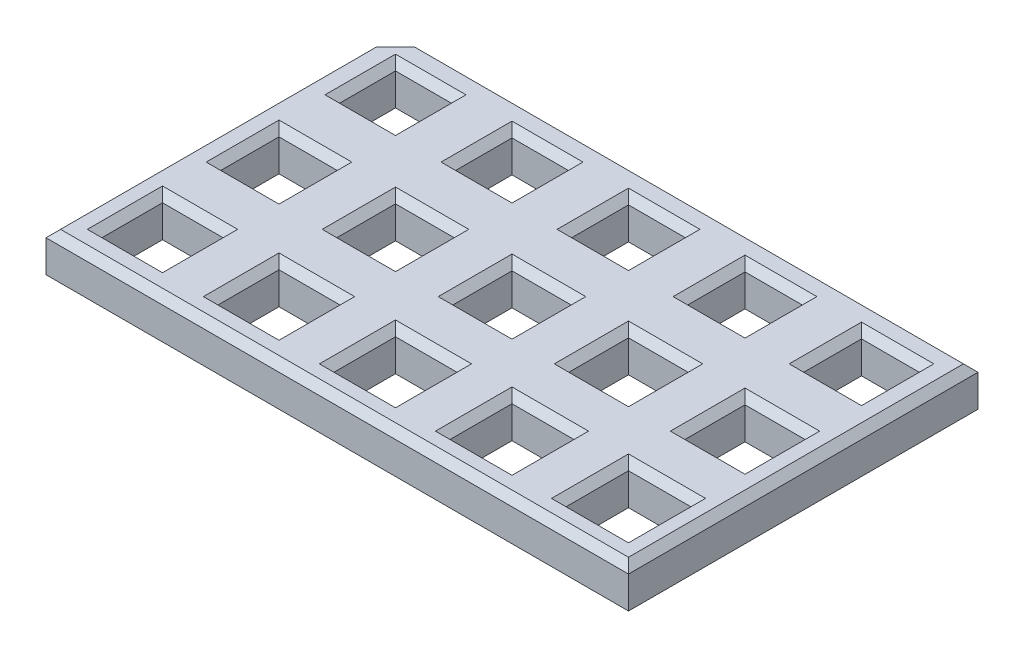
SolidWorks part; units mm, degrees
ref_plane "Front Plane" through (0, 0, 0) normal (0, 0, 1) x (1, 0, 0)
ref_plane "Top Plane" through (0, 0, 0) normal (0, 1, 0) x (1, 0, 0)
ref_plane "Right Plane" through (0, 0, 0) normal (1, 0, 0) x (0, 0, -1)
sketch "Sketch1" plane through (0, 0, 0) normal (0, 1, 0) x (1, 0, 0)
  line L1 (-1.5875, -1.5875) -> (1.5875, -1.5875)
  line L2 (-1.5875, -1.5875) -> (-1.5875, 1.5875)
  line L3 (-1.5875, 1.5875) -> (1.5875, 1.5875)
  line L4 (1.5875, -1.5875) -> (1.5875, 1.5875)
  line L5 (-1.5875, -1.5875) -> (1.5875, 1.5875) construction
  line L6 (-1.5875, 1.5875) -> (1.5875, -1.5875) construction
  line L7 (4.7498, -1.6002) -> (7.9502, -1.6002)
  line L8 (4.7498, -1.6002) -> (4.7498, 1.6002)
  line L9 (4.7498, 1.6002) -> (7.9502, 1.6002)
  line L10 (7.9502, -1.6002) -> (7.9502, 1.6002)
  line L11 (4.7498, -1.6002) -> (7.9502, 1.6002) construction
  line L12 (4.7498, 1.6002) -> (7.9502, -1.6002) construction
  line L13 (11.0871, -1.6129) -> (14.3129, -1.6129)
  line L14 (11.0871, -1.6129) -> (11.0871, 1.6129)
  line L15 (11.0871, 1.6129) -> (14.3129, 1.6129)
  line L16 (14.3129, -1.6129) -> (14.3129, 1.6129)
  line L17 (11.0871, -1.6129) -> (14.3129, 1.6129) construction
  line L18 (11.0871, 1.6129) -> (14.3129, -1.6129) construction
  line L19 (17.4244, -1.6256) -> (20.6756, -1.6256)
  line L20 (17.4244, -1.6256) -> (17.4244, 1.6256)
  line L21 (17.4244, 1.6256) -> (20.6756, 1.6256)
  line L22 (20.6756, -1.6256) -> (20.6756, 1.6256)
  line L23 (17.4244, -1.6256) -> (20.6756, 1.6256) construction
  line L24 (17.4244, 1.6256) -> (20.6756, -1.6256) construction
  line L25 (23.7617, -1.6383) -> (27.0383, -1.6383)
  line L26 (23.7617, -1.6383) -> (23.7617, 1.6383)
  line L27 (23.7617, 1.6383) -> (27.0383, 1.6383)
  line L28 (27.0383, -1.6383) -> (27.0383, 1.6383)
  line L29 (23.7617, -1.6383) -> (27.0383, 1.6383) construction
  line L30 (23.7617, 1.6383) -> (27.0383, -1.6383) construction
  line L31 (-1.524, 4.826) -> (1.524, 4.826)
  line L32 (-1.524, 4.826) -> (-1.524, 7.874)
  line L33 (-1.524, 7.874) -> (1.524, 7.874)
  line L34 (1.524, 4.826) -> (1.524, 7.874)
  line L35 (-1.524, 4.826) -> (1.524, 7.874) construction
  line L36 (-1.524, 7.874) -> (1.524, 4.826) construction
  line L37 (4.8133, 4.8133) -> (7.8867, 4.8133)
  line L38 (4.8133, 4.8133) -> (4.8133, 7.8867)
  line L39 (4.8133, 7.8867) -> (7.8867, 7.8867)
  line L40 (7.8867, 4.8133) -> (7.8867, 7.8867)
  line L41 (4.8133, 4.8133) -> (7.8867, 7.8867) construction
  line L42 (4.8133, 7.8867) -> (7.8867, 4.8133) construction
  line L43 (11.1506, 4.8006) -> (14.2494, 4.8006)
  line L44 (11.1506, 4.8006) -> (11.1506, 7.8994)
  line L45 (11.1506, 7.8994) -> (14.2494, 7.8994)
  line L46 (14.2494, 4.8006) -> (14.2494, 7.8994)
  line L47 (11.1506, 4.8006) -> (14.2494, 7.8994) construction
  line L48 (11.1506, 7.8994) -> (14.2494, 4.8006) construction
  line L49 (17.4879, 4.7879) -> (20.6121, 4.7879)
  line L50 (17.4879, 4.7879) -> (17.4879, 7.9121)
  line L51 (17.4879, 7.9121) -> (20.6121, 7.9121)
  line L52 (20.6121, 4.7879) -> (20.6121, 7.9121)
  line L53 (17.4879, 4.7879) -> (20.6121, 7.9121) construction
  line L54 (17.4879, 7.9121) -> (20.6121, 4.7879) construction
  line L55 (23.8252, 4.7752) -> (26.9748, 4.7752)
  line L56 (23.8252, 4.7752) -> (23.8252, 7.9248)
  line L57 (23.8252, 7.9248) -> (26.9748, 7.9248)
  line L58 (26.9748, 4.7752) -> (26.9748, 7.9248)
  line L59 (23.8252, 4.7752) -> (26.9748, 7.9248) construction
  line L60 (23.8252, 7.9248) -> (26.9748, 4.7752) construction
  line L61 (-1.651, -8.001) -> (1.651, -8.001)
  line L62 (-1.651, -8.001) -> (-1.651, -4.699)
  line L63 (-1.651, -4.699) -> (1.651, -4.699)
  line L64 (1.651, -8.001) -> (1.651, -4.699)
  line L65 (-1.651, -8.001) -> (1.651, -4.699) construction
  line L66 (-1.651, -4.699) -> (1.651, -8.001) construction
  line L67 (4.6863, -8.0137) -> (8.0137, -8.0137)
  line L68 (4.6863, -8.0137) -> (4.6863, -4.6863)
  line L69 (4.6863, -4.6863) -> (8.0137, -4.6863)
  line L70 (8.0137, -8.0137) -> (8.0137, -4.6863)
  line L71 (4.6863, -8.0137) -> (8.0137, -4.6863) construction
  line L72 (4.6863, -4.6863) -> (8.0137, -8.0137) construction
  line L73 (11.0236, -8.0264) -> (14.3764, -8.0264)
  line L74 (11.0236, -8.0264) -> (11.0236, -4.6736)
  line L75 (11.0236, -4.6736) -> (14.3764, -4.6736)
  line L76 (14.3764, -8.0264) -> (14.3764, -4.6736)
  line L77 (11.0236, -8.0264) -> (14.3764, -4.6736) construction
  line L78 (11.0236, -4.6736) -> (14.3764, -8.0264) construction
  line L79 (17.3609, -8.0391) -> (20.7391, -8.0391)
  line L80 (17.3609, -8.0391) -> (17.3609, -4.6609)
  line L81 (17.3609, -4.6609) -> (20.7391, -4.6609)
  line L82 (20.7391, -8.0391) -> (20.7391, -4.6609)
  line L83 (17.3609, -8.0391) -> (20.7391, -4.6609) construction
  line L84 (17.3609, -4.6609) -> (20.7391, -8.0391) construction
  line L85 (23.6982, -8.0518) -> (27.1018, -8.0518)
  line L86 (23.6982, -8.0518) -> (23.6982, -4.6482)
  line L87 (23.6982, -4.6482) -> (27.1018, -4.6482)
  line L88 (27.1018, -8.0518) -> (27.1018, -4.6482)
  line L89 (23.6982, -8.0518) -> (27.1018, -4.6482) construction
  line L90 (23.6982, -4.6482) -> (27.1018, -8.0518) construction
  line L91 (-3.175, 9.525) -> (28.575, 9.525)
  line L92 (-3.175, 9.525) -> (-3.175, -9.525)
  line L93 (-3.175, -9.525) -> (28.575, -9.525)
  line L94 (28.575, 9.525) -> (28.575, -9.525)
  point P0 (0, 0)
  point P6 (6.35, 0)
  point P11 (12.7, 0)
  point P16 (19.05, 0)
  point P21 (25.4, 0)
  point P26 (6.35, 6.35)
  point P27 (0, 6.35)
  point P36 (12.7, 6.35)
  point P41 (19.05, 6.35)
  point P46 (25.4, 6.35)
  point P51 (0, -6.35)
  point P56 (6.35, -6.35)
  point P61 (12.7, -6.35)
  point P66 (19.05, -6.35)
  point P71 (25.4, -6.35)
  dimension "D1" = 3.175
  dimension "D2" = 3.175
  dimension "D3" = 3.2004
  dimension "D4" = 3.2004
  dimension "D5" = 3.2258
  dimension "D6" = 3.2258
  dimension "D7" = 3.2512
  dimension "D8" = 3.2512
  dimension "D9" = 3.2766
  dimension "D10" = 3.2766
  dimension "D11" = 6.35
  dimension "D12" = 6.35
  dimension "D13" = 6.35
  dimension "D14" = 6.35
  dimension "D15" = 6.35
  dimension "D16" = 6.35
  dimension "D17" = 3.1496
  dimension "D18" = 3.1496
  dimension "D19" = 3.1242
  dimension "D20" = 3.1242
  dimension "D21" = 3.0988
  dimension "D22" = 3.0988
  dimension "D23" = 3.0734
  dimension "D24" = 3.0734
  dimension "D25" = 3.048
  dimension "D26" = 3.048
  dimension "D27" = 3.302
  dimension "D28" = 3.302
  dimension "D29" = 3.3274
  dimension "D30" = 3.3274
  dimension "D31" = 3.3528
  dimension "D32" = 3.3528
  dimension "D33" = 3.3782
  dimension "D34" = 3.3782
  dimension "D35" = 3.4036
  dimension "D36" = 3.4036
  dimension "D37" = 3.175
  dimension "D38" = 3.175
  dimension "D39" = 3.175
  dimension "D40" = 3.175
extrude "Boss-Extrude1" add sketch "Sketch1" along normal blind 2.54
chamfer "Chamfer1" distance 1.27 angle 45 1 edges at (-3.175, 1.27, -9.525)
chamfer "Chamfer2" distance 0.3969 angle 45 130 edges at (25.4, 0, 8.0518) (23.6982, 0, 6.35) (25.4, 0, 4.6482) (27.1018, 0, 6.35) (12.7, 0, 8.0264) (11.0236, 0, 6.35) (12.7, 0, 4.6736) (14.3764, 0, 6.35) (0, 0, 8.001) (-1.651, 0, 6.35) (0, 0, 4.699) (1.651, 0, 6.35) (19.05, 0, -4.7879) (17.4879, 0, -6.35) (19.05, 0, -7.9121) (20.6121, 0, -6.35) (6.35, 0, -4.8133) (4.8133, 0, -6.35) (6.35, 0, -7.8867) (7.8867, 0, -6.35) (25.4, 0, 1.6383) (23.7617, 0, 0) (25.4, 0, -1.6383) (27.0383, 0, 0) (12.7, 0, 1.6129) (11.0871, 0, 0) (12.7, 0, -1.6129) (14.3129, 0, 0) (0, 0, 1.5875) (-1.5875, 0, 0) (0, 0, -1.5875) (1.5875, 0, 0) (12.7, 0, 9.525) (28.575, 0, 0) (13.335, 0, -9.525) (-2.54, 0, -8.89) (-3.175, 0, 0.635) (6.35, 0, 1.6002) (4.7498, 0, 0) (6.35, 0, -1.6002) (7.9502, 0, 0) (19.05, 0, 1.6256) (17.4244, 0, 0) (19.05, 0, -1.6256) (20.6756, 0, 0) (0, 0, -4.826) (-1.524, 0, -6.35) (0, 0, -7.874) (1.524, 0, -6.35) (12.7, 0, -4.8006) (11.1506, 0, -6.35) (12.7, 0, -7.8994) (14.2494, 0, -6.35) (25.4, 0, -4.7752) (23.8252, 0, -6.35) (25.4, 0, -7.9248) (26.9748, 0, -6.35) (6.35, 0, 8.0137) (4.6863, 0, 6.35) (6.35, 0, 4.6863) (8.0137, 0, 6.35) (19.05, 0, 8.0391) (17.3609, 0, 6.35) (19.05, 0, 4.6609) (20.7391, 0, 6.35) (23.6982, 2.54, 6.35) (25.4, 2.54, 8.0518) (27.1018, 2.54, 6.35) (25.4, 2.54, 4.6482) (17.3609, 2.54, 6.35) (19.05, 2.54, 8.0391) (20.7391, 2.54, 6.35) (19.05, 2.54, 4.6609) (11.0236, 2.54, 6.35) (12.7, 2.54, 8.0264) (14.3764, 2.54, 6.35) (12.7, 2.54, 4.6736) (4.6863, 2.54, 6.35) (6.35, 2.54, 8.0137) (8.0137, 2.54, 6.35) (6.35, 2.54, 4.6863) (-1.651, 2.54, 6.35) (0, 2.54, 8.001) (1.651, 2.54, 6.35) (0, 2.54, 4.699) (23.8252, 2.54, -6.35) (25.4, 2.54, -4.7752) (26.9748, 2.54, -6.35) (25.4, 2.54, -7.9248) (17.4879, 2.54, -6.35) (19.05, 2.54, -4.7879) (20.6121, 2.54, -6.35) (19.05, 2.54, -7.9121) (11.1506, 2.54, -6.35) (12.7, 2.54, -4.8006) (14.2494, 2.54, -6.35) (12.7, 2.54, -7.8994) (4.8133, 2.54, -6.35) (6.35, 2.54, -4.8133) (7.8867, 2.54, -6.35) (6.35, 2.54, -7.8867) (-1.524, 2.54, -6.35) (0, 2.54, -4.826) (1.524, 2.54, -6.35) (0, 2.54, -7.874) (23.7617, 2.54, 0) (25.4, 2.54, 1.6383) (27.0383, 2.54, 0) (25.4, 2.54, -1.6383) (17.4244, 2.54, 0) (19.05, 2.54, 1.6256) (20.6756, 2.54, 0) (19.05, 2.54, -1.6256) (11.0871, 2.54, 0) (12.7, 2.54, 1.6129) (14.3129, 2.54, 0) (12.7, 2.54, -1.6129) (4.7498, 2.54, 0) (6.35, 2.54, 1.6002) (7.9502, 2.54, 0) (6.35, 2.54, -1.6002) (-1.5875, 2.54, 0) (0, 2.54, 1.5875) (1.5875, 2.54, 0) (0, 2.54, -1.5875) (28.575, 2.54, 0) (12.7, 2.54, 9.525) (-3.175, 2.54, 0.635) (-2.54, 2.54, -8.89) (13.335, 2.54, -9.525)
